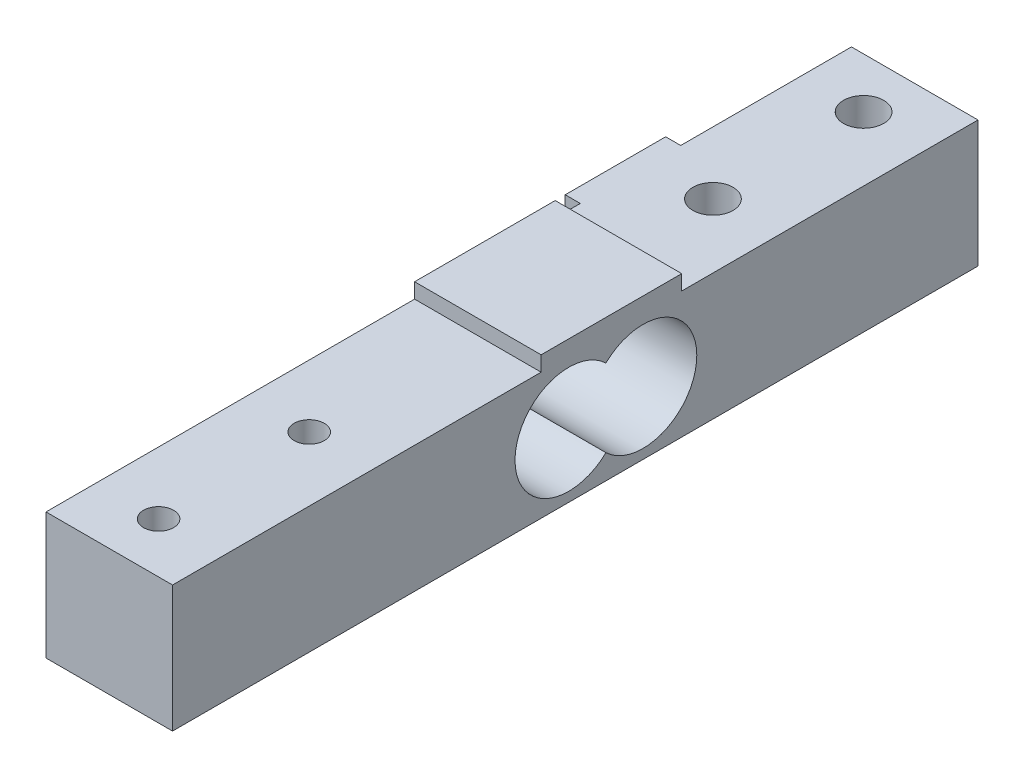
SolidWorks part; units mm, degrees
ref_plane "Plan de face" through (0, 0, 0) normal (0, 0, 1) x (1, 0, 0)
ref_plane "Plan de dessus" through (0, 0, 0) normal (0, 1, 0) x (1, 0, 0)
ref_plane "Plan de droite" through (0, 0, 0) normal (1, 0, 0) x (0, 0, -1)
sketch "Esquisse1" plane through (0, 0, 0) normal (0, 0, 1) x (1, 0, 0)
  line L1 (0, 0) -> (12.6, 0)
  line L2 (0, 0) -> (0, 12.6)
  line L3 (0, 12.6) -> (12.6, 12.6)
  line L4 (12.6, 0) -> (12.6, 12.6)
  dimension "D1" = 12.6
  dimension "D2" = 12.6
extrude "Boss.-Extru.1" add sketch "Esquisse1" along normal blind 80.2
sketch "Esquisse2" plane through (0, 12.6, 0) normal (0, 1, 0) x (1, 0, 0)
  line L0 (12.6, -80.2) -> (0, -80.2) construction
  line L1 (12.6, 0) -> (0, 0) construction
  circle A0 centre (6.2085, -75.2) radius 1.5
  circle A1 centre (6.2085, -60.2) radius 1.5
  circle A2 centre (6.2085, -20) radius 2
  circle A3 centre (6.2085, -5) radius 2
  dimension "D1" = 3
  dimension "D2" = 3
  dimension "D3" = 4
  dimension "D4" = 4
  dimension "D6" = 15
  dimension "D7" = 5
  dimension "D5" = 5
  dimension "D8" = 15
extrude "Enlèv. mat.-Extru.1" cut sketch "Esquisse2" against normal through all
sketch "Esquisse3" plane through (12.6, 0, 0) normal (1, 0, 0) x (0, 0, -1)
  line L0 (0, 0) -> (0, 12.6) construction
  line L1 (-80.2, 0) -> (-80.2, 12.6) construction
  line L2 (-80.2, 0) -> (0, 0) construction
  circle A0 centre (-40.75, 6.3) radius 5.35
  circle A1 centre (-33.35, 6.3) radius 5.35
  dimension "D1" = 10.7
  dimension "D2" = 10.7
  dimension "D3" = 33.35
  dimension "D4" = 39.45
  dimension "D5" = 7.4
  dimension "D6" = 6.3
extrude "Enlèv. mat.-Extru.4" cut sketch "Esquisse3" against normal through all contours A1 A0 | A0 A1 | A0 A1
sketch "Esquisse4" plane through (0, 12.6, 0) normal (0, 1, 0) x (1, 0, 0)
  line L0 (12.6, -80.2) -> (12.6, 0) construction
  line L1 (12.6, -43.5) -> (0, -43.5)
  line L2 (12.6, -43.5) -> (12.6, -29.5)
  line L3 (12.6, -29.5) -> (0, -29.5)
  line L4 (0, -43.5) -> (0, -29.5)
  line L5 (0, -80.2) -> (0, 0) construction
  circle A0 centre (6.2085, -20) radius 2 construction
  dimension "D1" = 14
  dimension "D2" = 9.5
extrude "Boss.-Extru.2" add sketch "Esquisse4" along normal blind 1.5
sketch "Esquisse5" plane through (0, 0, 0) normal (-1, 0, 0) x (0, 0, 1)
  line L0 (29.5, 12.6) -> (0, 12.6) construction
  line L1 (27, 12.6) -> (17, 12.6)
  line L2 (27, 12.6) -> (27, 0)
  line L3 (27, 0) -> (17, 0)
  line L4 (17, 12.6) -> (17, 0)
  line L5 (80.2, 0) -> (0, 0) construction
  line L6 (0, 12.6) -> (0, 0) construction
  point P8 (0, 6.3)
  dimension "D1" = 10
  dimension "D2" = 17
extrude "Boss.-Extru.3" add sketch "Esquisse5" along normal blind 1.5
